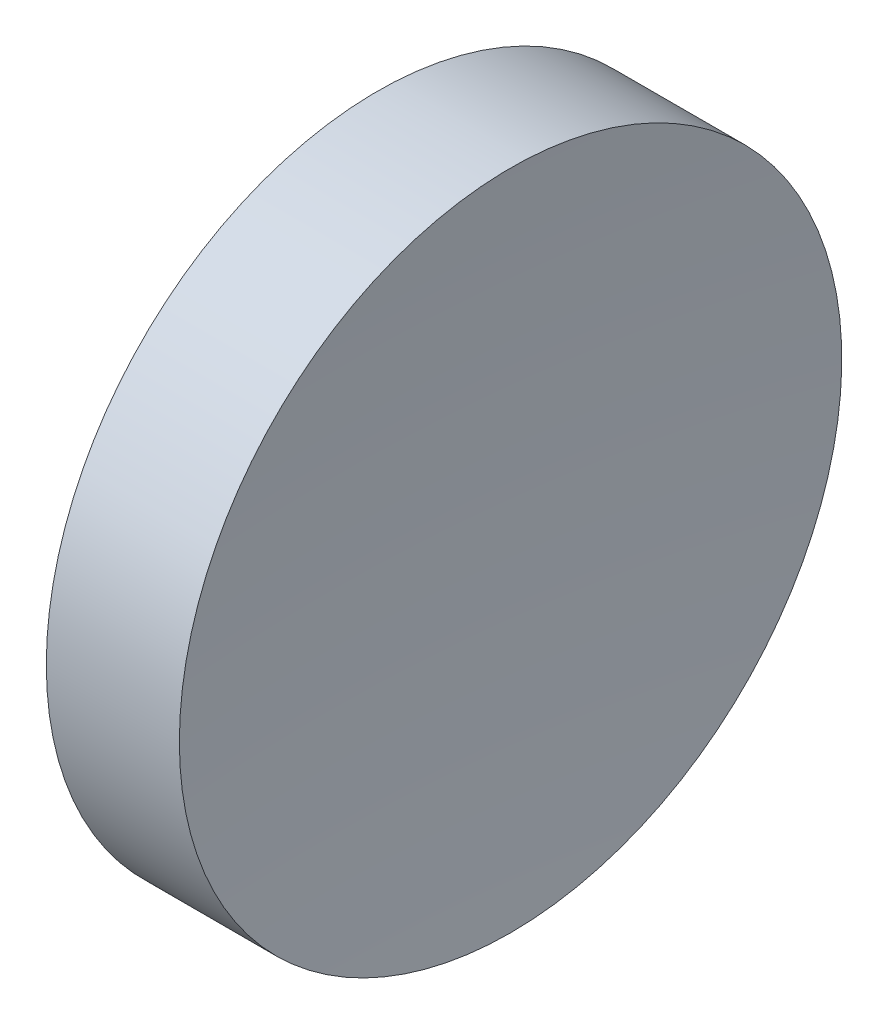
SolidWorks part; units mm, degrees
ref_plane "前视基准面" through (0, 0, 0) normal (0, 0, 1) x (1, 0, 0)
ref_plane "上视基准面" through (0, 0, 0) normal (0, 1, 0) x (1, 0, 0)
ref_plane "右视基准面" through (0, 0, 0) normal (1, 0, 0) x (0, 0, -1)
sketch "草图1" plane through (0, 0, 0) normal (0, 0, 1) x (1, 0, 0)
  line L0 (217.9703, 138.756) -> (265.5527, 138.756) construction
  line L1 (230.1853, 138.756) -> (230.1853, 163.756)
  line L2 (239.1853, 138.756) -> (230.1853, 138.756)
  line L3 (230.1853, 163.756) -> (240.2288, 163.756)
  arc A0 (240.2288, 163.756) -> (239.1853, 138.756) centre (539.1853, 138.756) ccw
  dimension "D1" = 300
  dimension "D2" = 10.0435
revolve "旋转1" add sketch "草图1" angle 360 about L0
